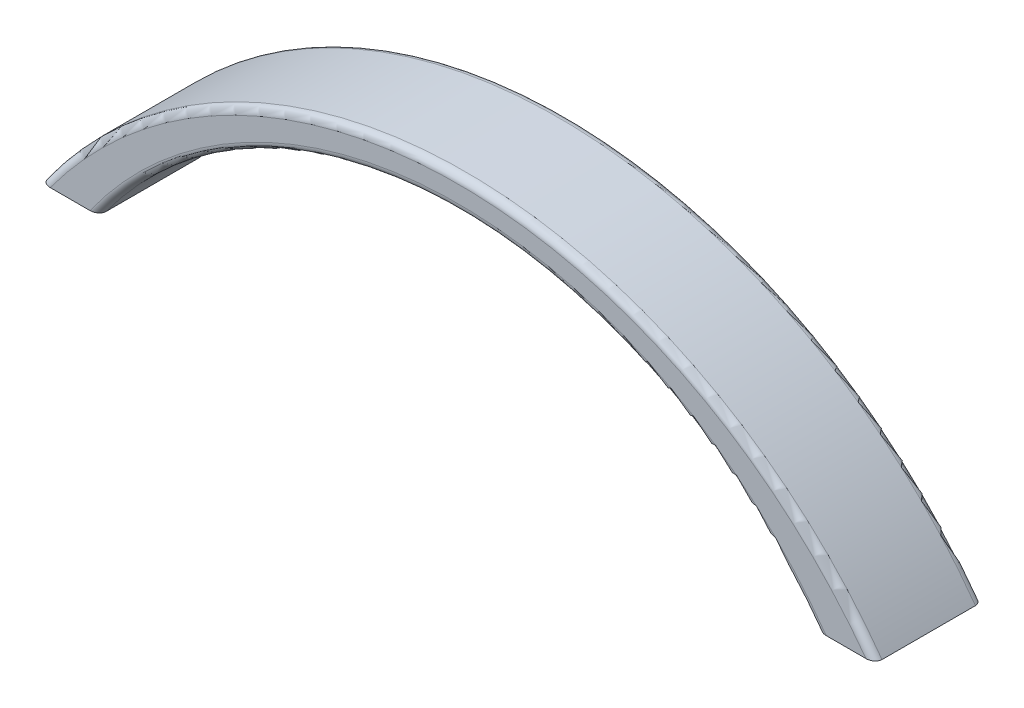
SolidWorks part; units mm, degrees
ref_plane "Ön Düzlem" through (0, 0, 0) normal (0, 0, 1) x (1, 0, 0)
ref_plane "Üst Düzlem" through (0, 0, 0) normal (0, 1, 0) x (1, 0, 0)
ref_plane "Sağ Düzlem" through (0, 0, 0) normal (1, 0, 0) x (0, 0, -1)
sketch "Sketch1" plane through (0, 0, 0) normal (0, 0, 1) x (1, 0, 0)
  line L0 (-50, 0) -> (-58, 0)
  line L1 (0, -54.9244) -> (0, 51.4832) construction
  line L2 (50, 0) -> (58, 0)
  arc A0 (-50, 0) -> (50, 0) centre (0, -36.3967) cw
  arc A1 (-58, 0) -> (58, 0) centre (0, -41.5081) cw
  dimension "D1" = 100
  dimension "D2" = 8
  dimension "D3" = 8
extrude "Boss-Extrude1" add sketch "Sketch1" along normal blind 15
fillet "Fillet1" radius 1 4 edges at (0, 25.4476, 0) (0, 25.4476, 15) (0, 29.8146, 15) (0, 29.8146, 0)
